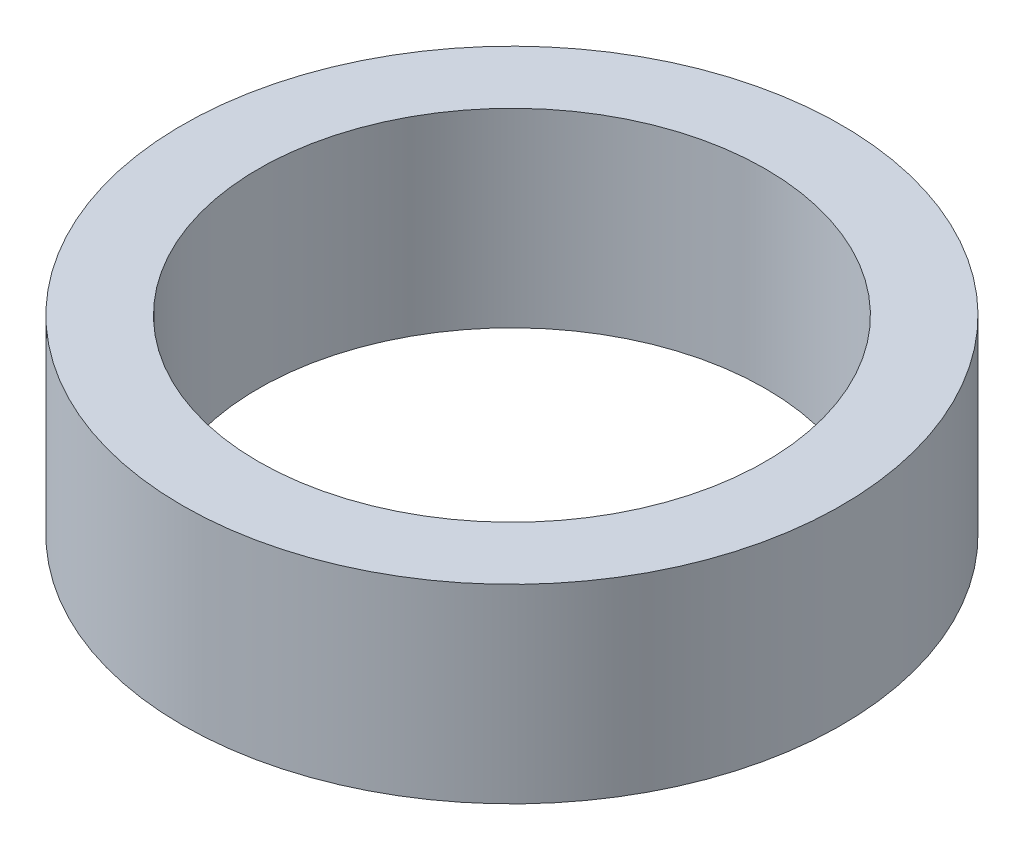
SolidWorks part; units mm, degrees
material "ABS"
ref_plane "Front Plane" through (0, 0, 0) normal (0, 0, 1) x (1, 0, 0)
ref_plane "Top Plane" through (0, 0, 0) normal (0, 1, 0) x (1, 0, 0)
ref_plane "Right Plane" through (0, 0, 0) normal (1, 0, 0) x (0, 0, -1)
sketch "Sketch1" plane through (0, 0, 0) normal (0, 1, 0) x (1, 0, 0)
  circle A0 centre (0, 0) radius 2
  circle A1 centre (0, 0) radius 2.6
  dimension "D1" = 4
  dimension "D2" = 5.2
extrude "Boss-Extrude1" add sketch "Sketch1" along normal blind 1.5
